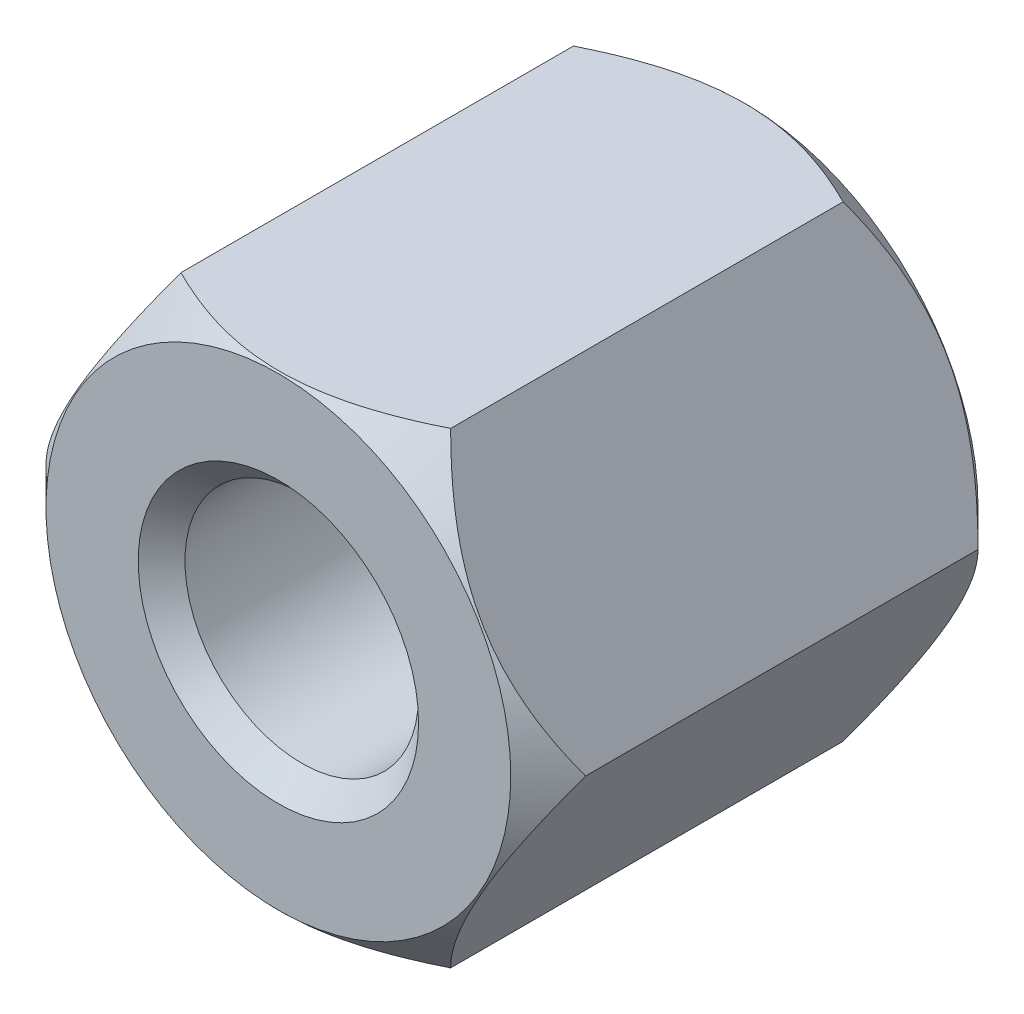
SolidWorks part; units mm, degrees
material "Brass"
ref_plane "Front Plane" through (0, 0, 0) normal (0, 0, 1) x (1, 0, 0)
ref_plane "Top Plane" through (0, 0, 0) normal (0, 1, 0) x (1, 0, 0)
ref_plane "Right Plane" through (0, 0, 0) normal (1, 0, 0) x (0, 0, -1)
ref_axis "Axis1" through (0, 0, 15.2667) along (0, 0, -1)
sketch "Sketch1" plane through (0, 0, 0) normal (0, 0, 1) x (1, 0, 0)
  line L1 (2.8868, 0) -> (1.4434, 2.5)
  line L2 (1.4434, 2.5) -> (-1.4434, 2.5)
  line L3 (-1.4434, 2.5) -> (-2.8868, 0)
  line L4 (-2.8868, 0) -> (-1.4434, -2.5)
  line L5 (-1.4434, -2.5) -> (1.4434, -2.5)
  line L6 (1.4434, -2.5) -> (2.8868, 0)
  circle A0 centre (0, 0) radius 2.5 construction
  dimension "D1" = 5
extrude "HEX" add sketch "Sketch1" along normal mid plane 5
hole_wizard "Tap Drill for M3x0.5 Tap1" positions "Sketch5" profile "Sketch6" hole size "M3x0.5" standard "BSI" end condition through all
sketch "Sketch5" plane through (0, 0, 2.5) normal (0, 0, 1) x (1, 0, 0)
  point P0 (0, 0)
sketch "Sketch6" plane through (0, 0, 2.5) normal (1, 0, 0) x (0, -1, 0)
  line L0 (0, 0) -> (0, 5)
  line L1 (0, 5) -> (1.25, 5)
  line L2 (1.25, 5) -> (1.25, 0)
  line L5 (1.25, 0) -> (0, 0)
  line L11 (0, -6.35) -> (0, 107.95) construction
  dimension "Thru Hole Dia." = 2.5
  dimension "Thru Hole Depth" = 5
sketch "Sketch7" plane through (0, 0, 0) normal (0, 1, 0) x (1, 0, 0)
  line L0 (-2.8868, 2.5) -> (-2.8868, 2.1)
  line L1 (-2.8868, -2.5) -> (-2.8868, 2.5) construction
  line L2 (-2.8868, 2.5) -> (-2.4868, 2.5)
  line L3 (-1.4434, 2.5) -> (-2.8868, 2.5) construction
  line L4 (-2.4868, 2.5) -> (-2.8868, 2.1)
  dimension "D1" = 0.4
revolve "HexChamfer" cut sketch "Sketch7" angle 360 about axis through (0, 0, 15.2667) along (0, 0, -1)
mirror "Mirror1" about plane through (0, 0, 0) normal (0, 0, 1) of "HexChamfer"
chamfer "InnerChamfer" distance 0.25 angle 45 2 edges at (1.25, 0, -2.5) (1.25, 0, 2.5)
